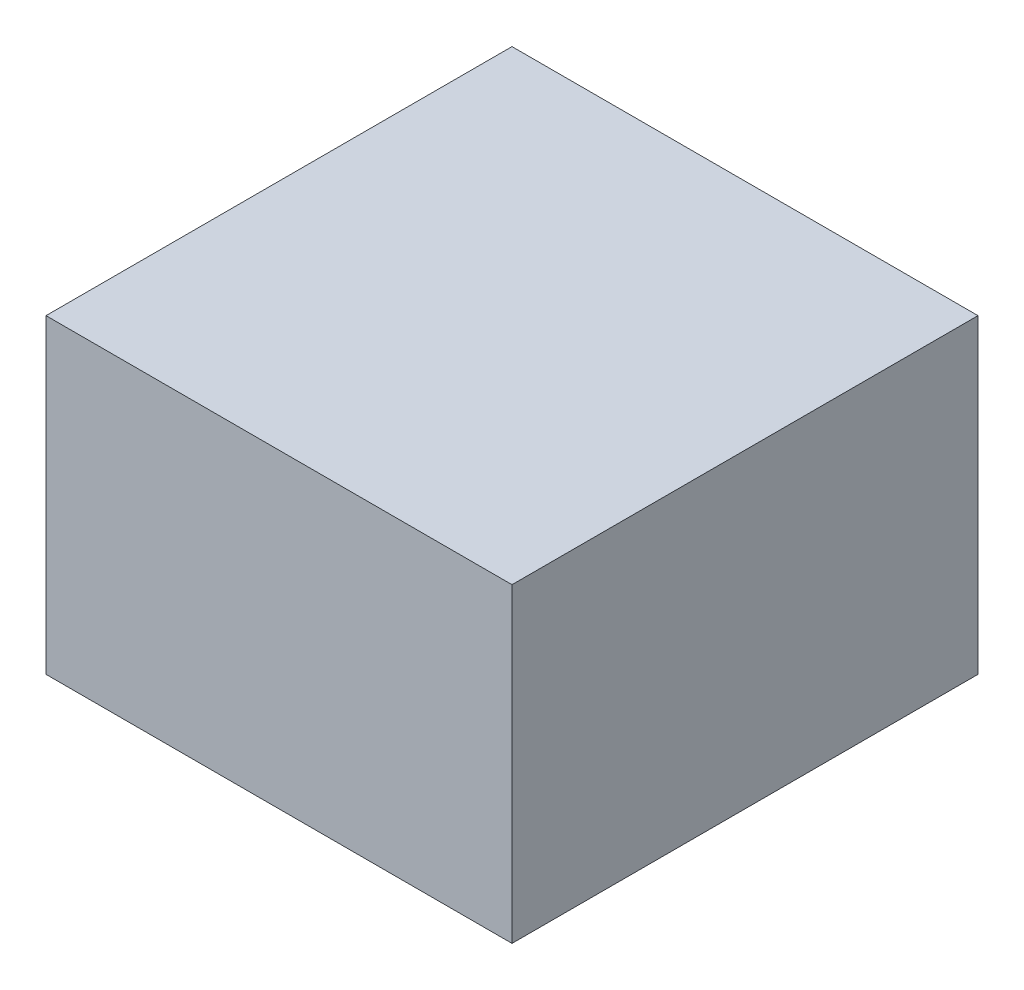
SolidWorks part; units mm, degrees
ref_plane "Alzado" through (0, 0, 0) normal (0, 0, 1) x (1, 0, 0)
ref_plane "Planta" through (0, 0, 0) normal (0, 1, 0) x (1, 0, 0)
ref_plane "Vista lateral" through (0, 0, 0) normal (1, 0, 0) x (0, 0, -1)
sketch "Croquis1" plane through (0, 0, 0) normal (0, 1, 0) x (1, 0, 0)
  line L1 (-15, 15) -> (15, 15)
  line L2 (-15, 15) -> (-15, -15)
  line L3 (-15, -15) -> (15, -15)
  line L4 (15, 15) -> (15, -15)
  line L5 (-15, 15) -> (15, -15) construction
  line L6 (-15, -15) -> (15, 15) construction
  point P0 (0, 0)
  dimension "D1" = 30
  dimension "D2" = 30
extrude "Saliente-Extruir1" add sketch "Croquis1" along normal blind 20
